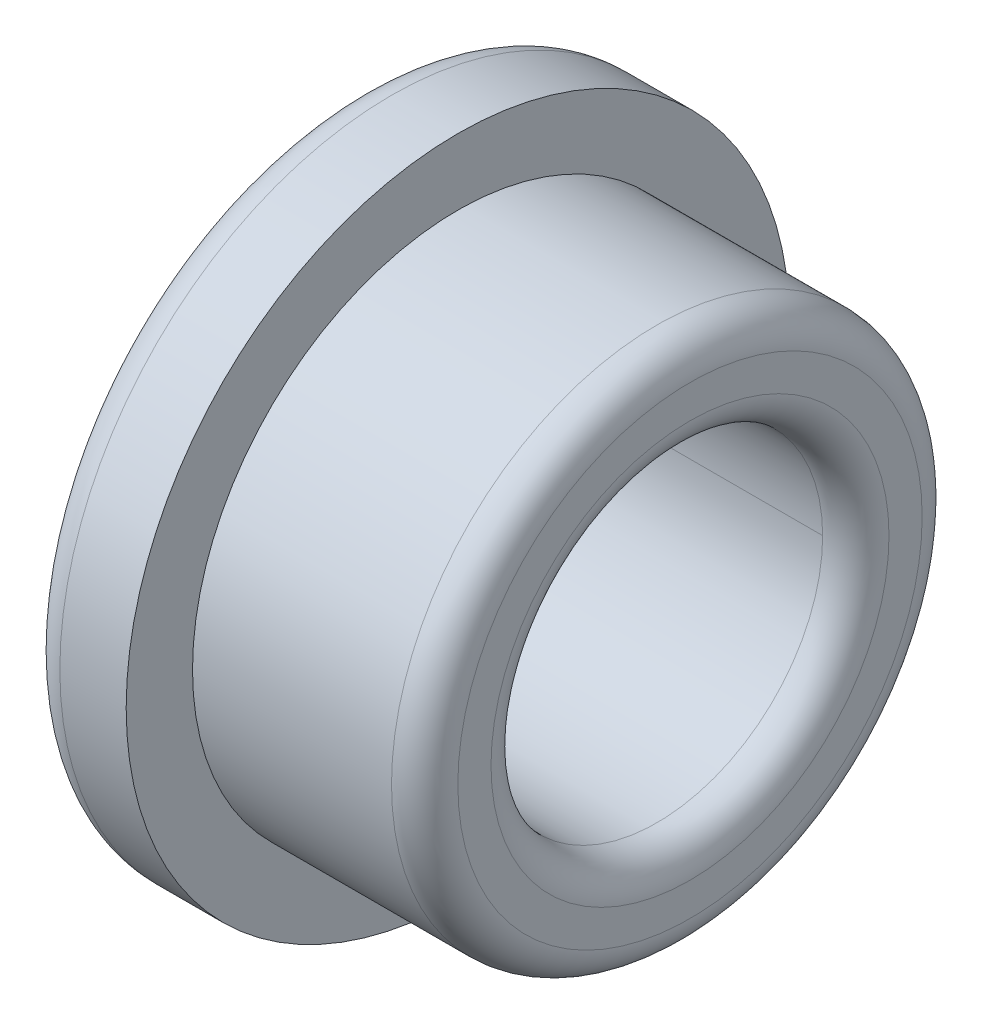
SolidWorks part; units mm, degrees
material "Brass"
ref_plane "Front Plane" through (0, 0, 0) normal (0, 0, 1) x (1, 0, 0)
ref_plane "Top Plane" through (0, 0, 0) normal (0, 1, 0) x (1, 0, 0)
ref_plane "Right Plane" through (0, 0, 0) normal (1, 0, 0) x (0, 0, -1)
sketch "Sketch1" plane through (0, 0, 0) normal (0, 0, 1) x (1, 0, 0)
  line L0 (-1, 0) -> (-7, 0)
  line L1 (-7, 0) -> (-7, -2)
  line L2 (-7, -2) -> (-9, -2)
  line L3 (-10, -1) -> (-10, 2)
  line L4 (-9, 3) -> (-1, 3)
  line L5 (0, 2) -> (0, 1)
  line L6 (-10, 8) -> (0, 8) construction
  arc A0 (-1, 0) -> (0, 1) centre (-1, 1) ccw
  arc A1 (-1, 3) -> (0, 2) centre (-1, 2) cw
  arc A2 (-9, -2) -> (-10, -1) centre (-9, -1) cw
  arc A3 (-10, 2) -> (-9, 3) centre (-9, 2) cw
  point P13 (0, 0)
  point P16 (0, 3)
  point P19 (-10, -2)
  point P22 (-10, 3)
  dimension "D7" = 1
  dimension "D1" = 10
  dimension "D2" = 3
  dimension "D4" = 5
  dimension "D5" = 8
  dimension "D6" = 2
revolve "Revolve1" add sketch "Sketch1" angle 360 about L6
sketch "Sketch2" plane through (0, 0, 0) normal (0, 0, 1) x (1, 0, 0)
  line L6 (2.6125, 8) -> (-12.207, 8)
  line L7 (-10, 17) -> (-10, -1) construction
  dimension "D1" = 14.8195
  dimension "D2" = 8
  dimension "D3" = 2.207
split line "Split Line4"
